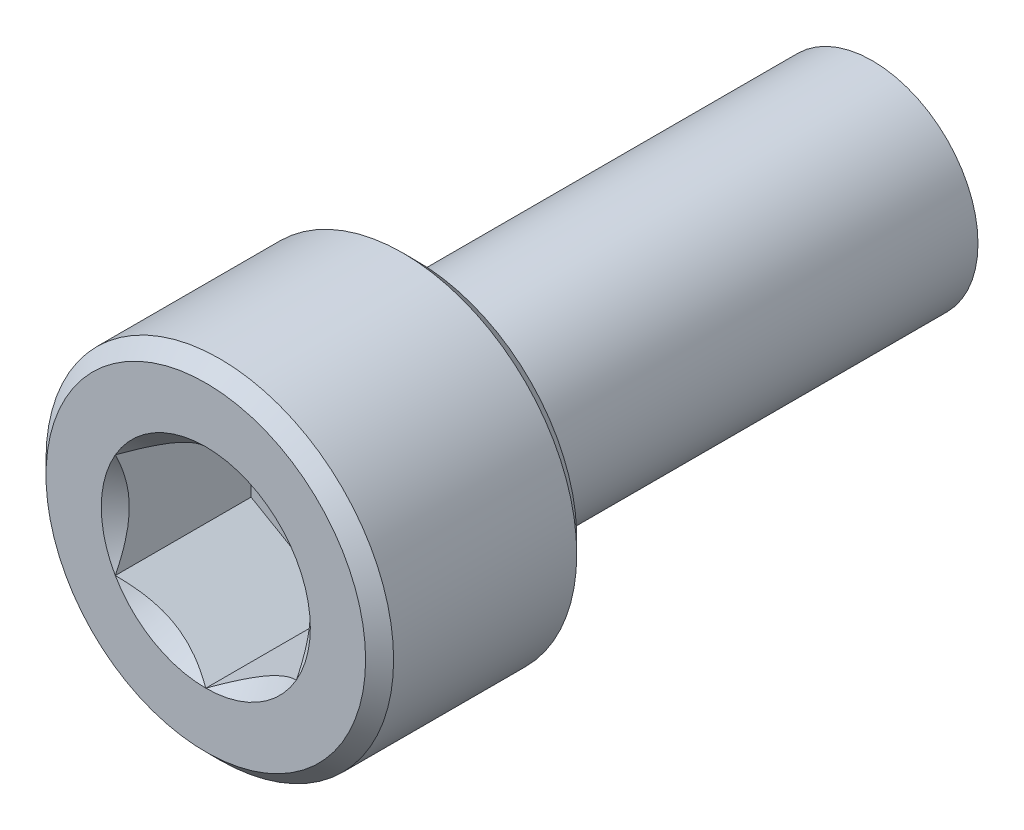
SolidWorks part; units mm, degrees
ref_plane "Front Plane" through (0, 0, 0) normal (0, 0, 1) x (1, 0, 0)
ref_plane "Top Plane" through (0, 0, 0) normal (0, 1, 0) x (1, 0, 0)
ref_plane "Right Plane" through (0, 0, 0) normal (1, 0, 0) x (0, 0, -1)
ref_plane "Plane1" through (0, 0, 0) normal (0, -1, 0) x (1, 0, 0)
sketch "Sketch1" plane through (0, 0, 0) normal (0, -1, 0) x (1, 0, 0)
  line L0 (13.7972, 6.6656) -> (10.3682, 6.6656)
  line L1 (10.3682, 6.6656) -> (10.3682, 2.5)
  line L2 (10.3682, 2.5) -> (13.7972, 2.5)
  line L3 (13.7972, 2.5) -> (13.7972, 6.6656)
  line L4 (10.3682, 6.6656) -> (10.3682, 2.5) construction
  point P4 (0, 0)
  dimension "D1" = 3.429
  dimension "D2" = 4.1656
revolve "Revolve1" add sketch "Sketch1" angle 360 about L4
sketch "Sketch2" plane through (0, 0, 2.5) normal (0, 0, -1) x (-1, 0, 0)
  circle A0 centre (-10.3682, 0) radius 2.0828
  point P2 (0, 0)
  dimension "D1" = 4.1656
extrude "Boss-Extrude1" add sketch "Sketch2" along normal blind 9.525
ref_plane "Plane2" through (0, 0, 3.9867) normal (0, 0, -1) x (-1, 0, 0)
sketch "Sketch3" plane through (0, 0, 3.9867) normal (0, 0, -1) x (-1, 0, 0)
  line L0 (-10.3682, -2.0622) -> (-8.5823, -1.0311)
  line L1 (-8.5823, -1.0311) -> (-8.5823, 1.0311)
  line L2 (-8.5823, 1.0311) -> (-10.3682, 2.0622)
  line L3 (-10.3682, 2.0622) -> (-12.1541, 1.0311)
  line L4 (-12.1541, 1.0311) -> (-12.1541, -1.0311)
  line L5 (-12.1541, -1.0311) -> (-10.3682, -2.0622)
  dimension "D1" = 1.7859
  dimension "D2" = 3.5719
  dimension "D3" = 1.0311
  dimension "D4" = 3.0933
  dimension "D5" = 4.1244
extrude "Cut-Extrude1" cut sketch "Sketch3" against normal up to surface (2.6789 mm away) up to face at (6.9392, 0, 6.6656)
chamfer "Chamfer1" distance 0.2763 angle 45 2 edges at (6.9392, 0, 2.5) (6.9392, 0, 6.6656)
chamfer "Chamfer2" distance 0.7696 angle 35 1 edges at (8.2854, 0, -7.025)
sketch "Sketch4" plane through (0, 0, 0) normal (0, 1, 0) x (1, 0, 0)
  line L0 (8.5823, -6.3893) -> (8.306, -6.6656)
  line L1 (7.2155, -6.6656) -> (13.5209, -6.6656) construction
  line L2 (8.306, -6.6656) -> (8.5823, -6.6656)
  line L3 (8.5823, -6.6656) -> (8.5823, -6.3893)
  line L4 (13.7972, -6.3893) -> (6.9392, -6.3893) construction
  point P4 (8.2972, -6.3893)
  point P8 (8.5823, -6.6656)
  point P10 (0, 0)
  point P12 (8.3084, -6.6656)
  dimension "D1" = 45
ref_plane "Plane3" through (10.3682, 0, 0) normal (-1, 0, 0) x (0, 0, 1)
ref_axis "Axis1" through (10.3682, 0, 6.7995) along (0, 0, -1)
revolve "Cut-Revolve1" cut sketch "Sketch4" angle 360 about axis through (10.3682, 0, 6.7995) along (0, 0, -1)
